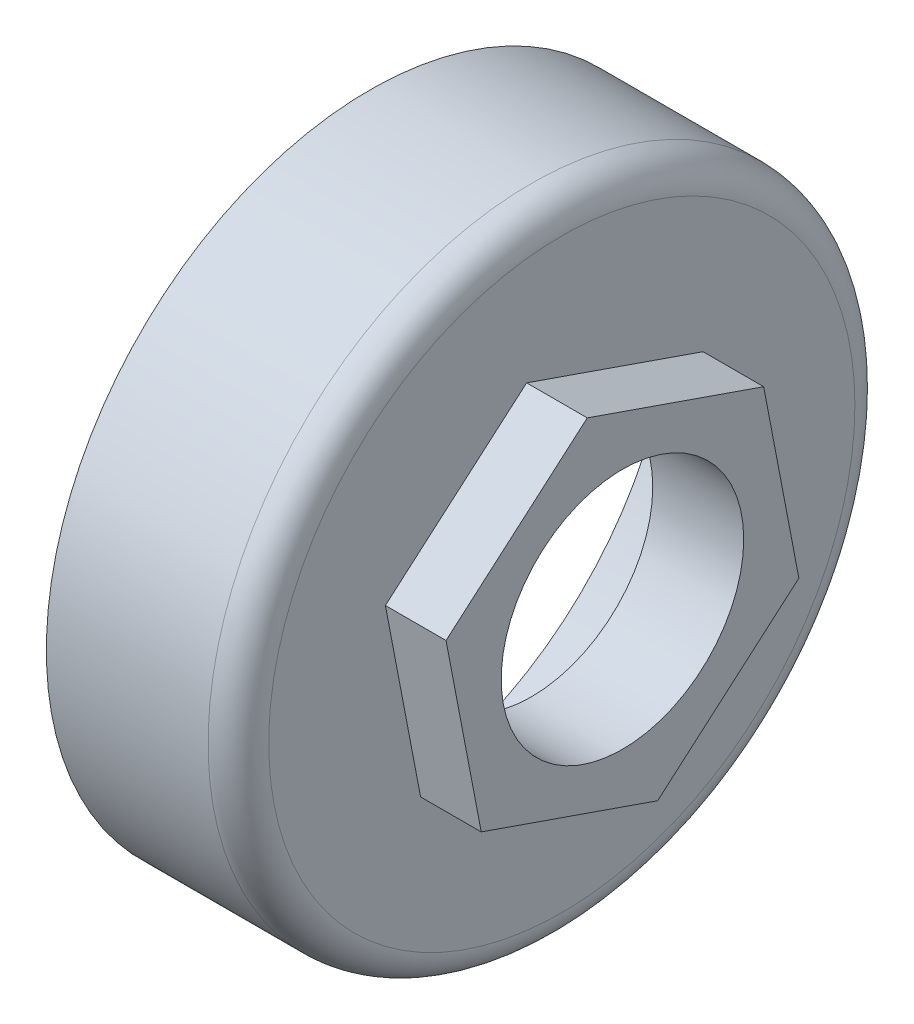
SolidWorks part; units mm, degrees
ref_plane "Front Plane" through (0, 0, 0) normal (0, 0, 1) x (1, 0, 0)
ref_plane "Top Plane" through (0, 0, 0) normal (0, 1, 0) x (1, 0, 0)
ref_plane "Right Plane" through (0, 0, 0) normal (1, 0, 0) x (0, 0, -1)
sketch "Sketch1" plane through (0, 0, 0) normal (1, 0, 0) x (0, 0, -1)
  circle A0 centre (0, 0) radius 32
  dimension "D1" = 64
extrude "Boss-Extrude1" add sketch "Sketch1" along normal blind 19
sketch "Sketch5" plane through (0, 0, 0) normal (-1, 0, 0) x (0, 0, 1)
  circle A0 centre (0, 0) radius 30
  dimension "D1" = 60
extrude "Cut-Extrude1" cut sketch "Sketch5" against normal blind 16
fillet "Fillet1" radius 3 1 edges at (19, 0, -32)
sketch "Sketch6" plane through (19, 0, 0) normal (1, 0, 0) x (0, 0, -1)
  line L1 (-17.4541, 6.0571) -> (-13.9727, -12.0871)
  line L2 (-13.9727, -12.0871) -> (3.4814, -18.1442)
  line L3 (3.4814, -18.1442) -> (17.4541, -6.0571)
  line L4 (17.4541, -6.0571) -> (13.9727, 12.0871)
  line L5 (13.9727, 12.0871) -> (-3.4814, 18.1442)
  line L6 (-3.4814, 18.1442) -> (-17.4541, 6.0571)
  circle A0 centre (0, 0) radius 16 construction
  dimension "D1" = 32
extrude "Boss-Extrude2" add sketch "Sketch6" along normal blind 6
sketch "Sketch7" plane through (25, 0, 0) normal (1, 0, 0) x (0, 0, -1)
  circle A0 centre (0, 0) radius 12
  dimension "D1" = 24
extrude "Cut-Extrude2" cut sketch "Sketch7" against normal through all
